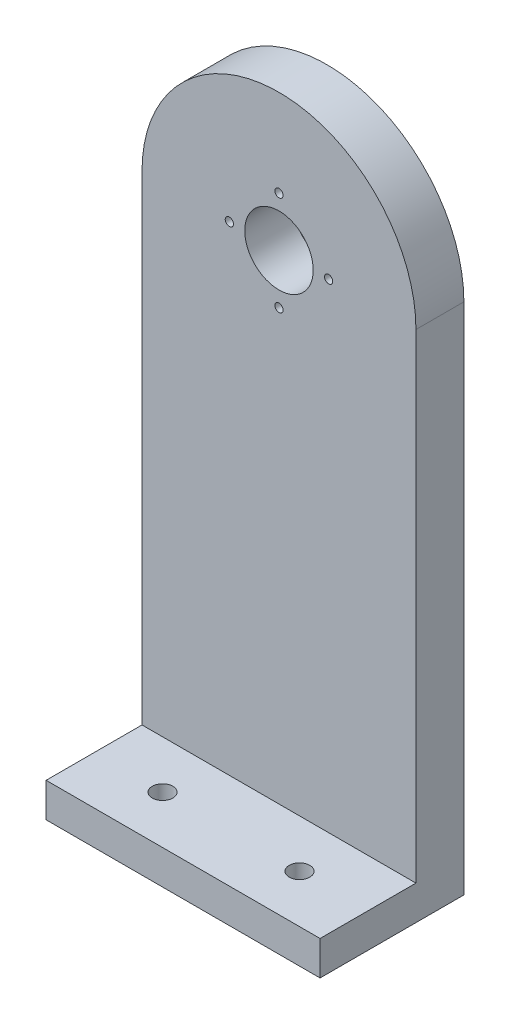
SolidWorks part; units mm, degrees
material "PBT General Purpose"
ref_plane "Front" through (0, 0, 0) normal (0, 0, 1) x (1, 0, 0)
ref_plane "Top" through (0, 0, 0) normal (0, 1, 0) x (1, 0, 0)
ref_plane "Right" through (0, 0, 0) normal (1, 0, 0) x (0, 0, -1)
sketch "Sketch1" plane through (0, 0, 0) normal (0, 0, 1) x (1, 0, 0)
  line L0 (0, 0) -> (0, -75) construction
  line L1 (20, 0) -> (20, -75)
  line L2 (-20, 0) -> (-20, -75)
  line L3 (-7.25, 0) -> (0, 0) construction
  line L4 (0, 0) -> (0, 7.25) construction
  line L5 (-20, -75) -> (20, -75)
  line L6 (7.25, 0) -> (0, 0) construction
  line L7 (0, 0) -> (0, -7.25) construction
  arc A0 (20, 0) -> (-20, 0) centre (0, 0) ccw
  circle A2 centre (0, 0) radius 5
  circle A3 centre (0, 7.25) radius 0.6
  circle A4 centre (-7.25, 0) radius 0.6
  circle A5 centre (0, -7.25) radius 0.6
  circle A6 centre (7.25, 0) radius 0.6
  point P0 (0, -37.5)
  dimension "D3" = 10
  dimension "D5" = 1.2
  dimension "D1" = 75
  dimension "D2" = 40
  dimension "D4" = 7.25
extrude "Boss-Extrude1" add sketch "Sketch1" along normal blind 7
sketch "Sketch2" plane through (0, 0, 7) normal (0, 0, 1) x (1, 0, 0)
  line L0 (-20, 0) -> (-20, -75) construction
  line L1 (-20, -70) -> (20, -70)
  line L2 (-20, -70) -> (-20, -75)
  line L3 (-20, -75) -> (20, -75)
  line L4 (20, -70) -> (20, -75)
  line L5 (20, -75) -> (20, 0) construction
  line L6 (-20, -75) -> (20, -75) construction
  dimension "D1" = 5
extrude "Boss-Extrude2" add sketch "Sketch2" along normal blind 14
sketch "Sketch3" plane through (0, -70, 0) normal (0, 1, 0) x (1, 0, 0)
  line L0 (10, -14) -> (-10, -14) construction
  line L1 (-10, -14) -> (-20, -14) construction
  line L2 (-20, -21) -> (-20, -7) construction
  line L3 (0, -14) -> (0, -7) construction
  line L4 (20, -7) -> (-20, -7) construction
  circle A0 centre (-10, -14) radius 1.5
  circle A1 centre (10, -14) radius 1.5
  dimension "D2" = 3
  dimension "D1" = 20
extrude "Cut-Extrude1" cut sketch "Sketch3" against normal through all
